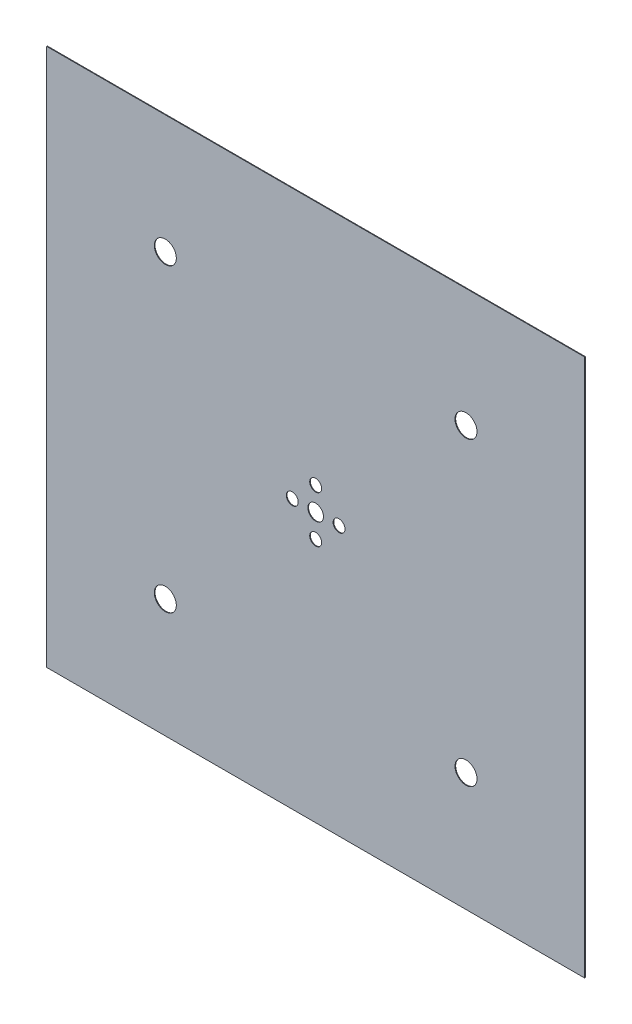
SolidWorks part; units mm, degrees
ref_plane "Front" through (0, 0, 0) normal (0, 0, 1) x (1, 0, 0)
ref_plane "Top" through (0, 0, 0) normal (0, 1, 0) x (1, 0, 0)
ref_plane "Right" through (0, 0, 0) normal (1, 0, 0) x (0, 0, -1)
sketch "Sketch2" plane through (0, 0, 0) normal (0, 0, 1) x (1, 0, 0)
  line L0 (-1610, 0) -> (1610, 0) construction
  line L1 (-1610, 1610) -> (1610, 1610)
  line L2 (-1610, 1610) -> (-1610, -1610)
  line L3 (-1610, -1610) -> (1610, -1610)
  line L4 (1610, 1610) -> (1610, -1610)
  line L5 (-1610, 1610) -> (1610, -1610) construction
  line L6 (-1610, -1610) -> (1610, 1610) construction
  line L7 (0, 1610) -> (0, -1610) construction
  circle A0 centre (0, 0) radius 46.75
  circle A1 centre (0, 140) radius 35.6375
  circle A2 centre (-900, 900) radius 65.8
  circle A3 centre (0, -140) radius 35.6375
  circle A4 centre (-900, -900) radius 65.8
  circle A5 centre (140, 0) radius 35.6375
  circle A6 centre (-140, 0) radius 35.6375
  circle A7 centre (900, -900) radius 65.8
  circle A8 centre (900, 900) radius 65.8
  point P0 (0, 0)
  dimension "D3" = 93.5
  dimension "D4" = 71.275
  dimension "D6" = 131.6
  dimension "D1" = 3220
  dimension "D2" = 3220
  dimension "D5" = 140
  dimension "D7" = 900
extrude "Boss-Extrude1" add sketch "Sketch2" along normal blind 4
